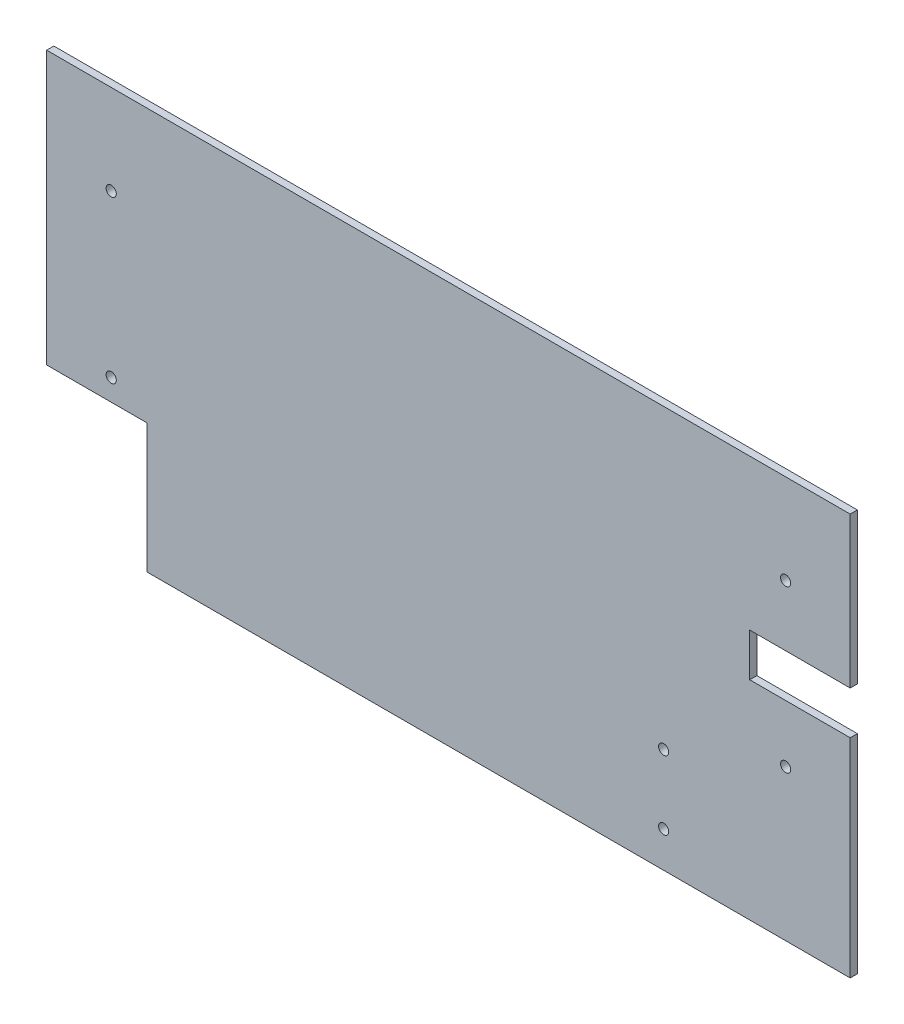
SolidWorks part; units mm, degrees
ref_plane "Front Plane" through (0, 0, 0) normal (0, 0, 1) x (1, 0, 0)
ref_plane "Top Plane" through (0, 0, 0) normal (0, 1, 0) x (1, 0, 0)
ref_plane "Right Plane" through (0, 0, 0) normal (1, 0, 0) x (0, 0, -1)
sketch "Sketch1" plane through (0, 0, 0) normal (0, 0, 1) x (1, 0, 0)
  line L0 (0, 88.9) -> (0, -88.9) construction
  line L1 (177.8, -88.9) -> (-177.8, -88.9)
  line L2 (177.8, -88.9) -> (177.8, 88.9)
  line L3 (177.8, 88.9) -> (-177.8, 88.9)
  line L4 (-177.8, -88.9) -> (-177.8, 88.9)
  line L5 (177.8, -88.9) -> (-177.8, 88.9) construction
  line L6 (177.8, 88.9) -> (-177.8, -88.9) construction
  line L7 (-177.8, -88.9) -> (-133.35, -88.9)
  line L8 (-177.8, -88.9) -> (-177.8, -31.75)
  line L9 (-177.8, -31.75) -> (-133.35, -31.75)
  line L10 (-133.35, -88.9) -> (-133.35, -31.75)
  line L12 (177.8, 3.175) -> (133.35, 3.175)
  line L13 (177.8, 3.175) -> (177.8, 22.225)
  line L14 (177.8, 22.225) -> (133.35, 22.225)
  line L15 (133.35, 3.175) -> (133.35, 22.225)
  circle A0 centre (-149.225, 49.2125) radius 2.25
  circle A1 centre (-149.225, -22.225) radius 2.25
  circle A2 centre (149.225, 49.2125) radius 2.25
  circle A3 centre (149.225, -22.225) radius 2.25
  circle A4 centre (95.25, -73.025) radius 2.25
  circle A5 centre (95.25, -42.545) radius 2.25
  point P0 (0, 0)
  dimension "D3" = 4.5
  dimension "D8" = 4.5
  dimension "D11" = 66.675
  dimension "D15" = 4.5
  dimension "D16" = 4.5
  dimension "D1" = 355.6
  dimension "D2" = 177.8
  dimension "D4" = 39.6875
  dimension "D5" = 28.575
  dimension "D6" = 28.575
  dimension "D7" = 111.125
  dimension "D9" = 120.65
  dimension "D10" = 44.45
  dimension "D12" = 19.05
  dimension "D13" = 82.55
  dimension "D14" = 161.925
  dimension "D17" = 30.48
  dimension "D18" = 82.55
  dimension "D19" = 44.45
extrude "Boss-Extrude1" add sketch "Sketch1" against normal blind 3.175 contours L12 L15 L14 L2 L3 L4 L9 L10 L1 A5 A4 A2 A1 A0 A3
